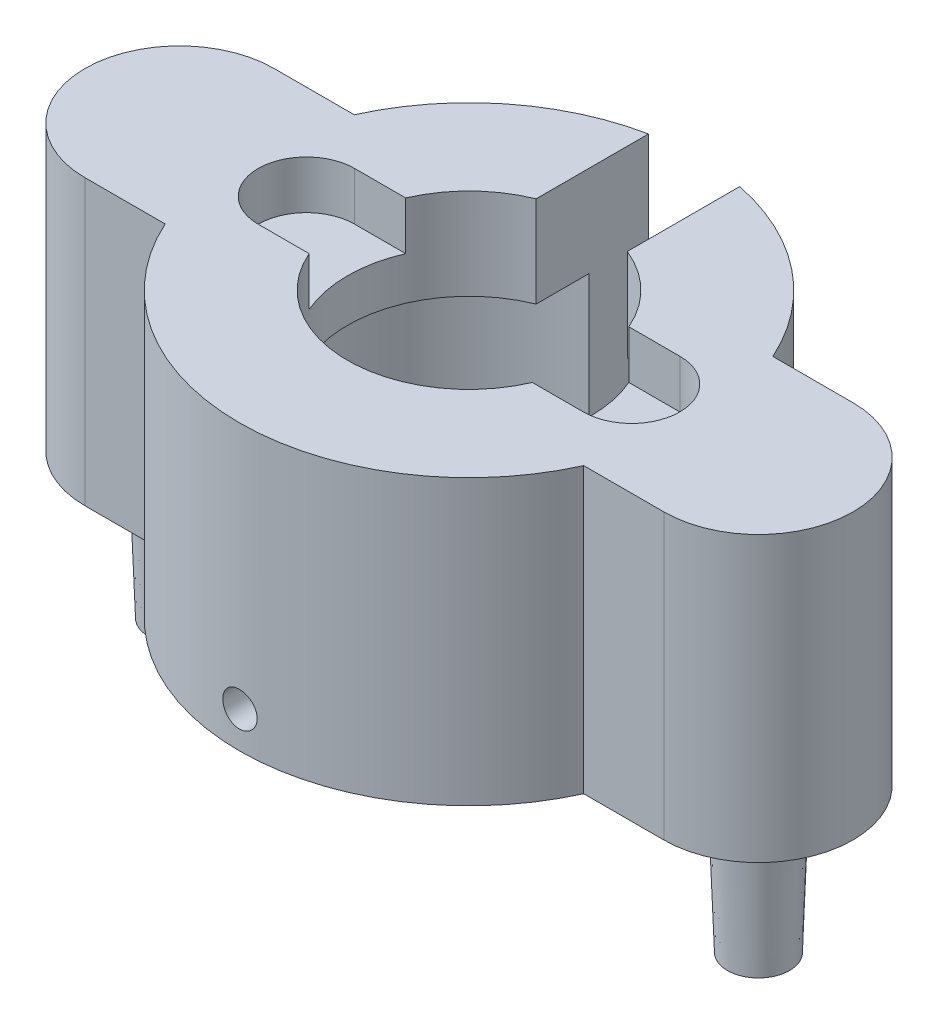
SolidWorks part; units mm, degrees
ref_plane "Front Plane" through (0, 0, 0) normal (0, 0, 1) x (1, 0, 0)
ref_plane "Top Plane" through (0, 0, 0) normal (0, 1, 0) x (1, 0, 0)
ref_plane "Right Plane" through (0, 0, 0) normal (1, 0, 0) x (0, 0, -1)
sketch "Sketch1" plane through (0, 0, 0) normal (0, 1, 0) x (1, 0, 0)
  line L0 (-19.05, 6.223) -> (-13.7723, 6.223)
  line L1 (19.05, 6.223) -> (13.7723, 6.223)
  line L2 (19.05, -6.223) -> (13.7723, -6.223)
  line L3 (-19.05, -6.223) -> (-13.7723, -6.223)
  circle A0 centre (0, 0) radius 11.303
  circle A1 centre (0, 0) radius 15.113 construction
  circle A2 centre (19.05, 0) radius 2.413 construction
  circle A3 centre (-19.05, 0) radius 2.413 construction
  circle A4 centre (19.05, 0) radius 6.223 construction
  circle A5 centre (-19.05, 0) radius 6.223 construction
  arc A6 (-19.05, 6.223) -> (-19.05, -6.223) centre (-19.05, 0) ccw
  arc A7 (19.05, 6.223) -> (19.05, -6.223) centre (19.05, 0) cw
  arc A8 (-13.7723, 6.223) -> (13.7723, 6.223) centre (0, 0) cw
  arc A9 (-13.7723, -6.223) -> (13.7723, -6.223) centre (0, 0) ccw
  dimension "D1" = 22.606
  dimension "D2" = 3.81
  dimension "D3" = 4.826
  dimension "D4" = 19.05
  dimension "D6" = 3.81
  dimension "D5" = 19.05
extrude "Boss-Extrude1" add sketch "Sketch1" along normal blind 12.7
ref_plane "Plane1" through (0, 0, 15.113) normal (0, 0, 1) x (1, 0, 0)
hole_wizard "#4-40 Tapped Hole1" positions "Sketch3" profile "Sketch4" tap size "#4-40" standard "Ansi Inch" end condition through all
sketch "Sketch3" plane through (0, 0, 15.113) normal (0, 0, 1) x (1, 0, 0)
  line L0 (-13.7723, 0) -> (13.7723, 0) construction
  point P1 (0, 2.3813)
  dimension "D1" = 2.3813
sketch "Sketch4" plane through (0, 2.3813, 15.113) normal (1, 0, 0) x (0, -1, 0)
  line L0 (0, 0) -> (0, 30.226)
  line L1 (0, 30.226) -> (1.1303, 30.226)
  line L2 (1.1303, 30.226) -> (1.1303, 0)
  line L5 (1.1303, 0) -> (0, 0)
  line L11 (0, -6.35) -> (0, 107.95) construction
  dimension "Thread Major Dia." = 2.2606
  dimension "Thru Tap Drill Depth" = 30.226
ref_plane "Plane2" through (25.273, 0, 0) normal (1, 0, 0) x (0, 0, -1)
hole_wizard "#4-40 Tapped Hole3" [suppressed] positions "Sketch8" profile "Sketch9" tap size "#4-40" standard "Ansi Inch"
sketch "Sketch8" plane through (0, 9.525, 0) normal (0, 1, 0) x (-1, 0, 0)
  point P0 (12.7, 0)
  dimension "D1" = 12.7
sketch "Sketch9" plane through (-12.7, 9.525, 0) normal (1, 0, 0) x (0, 0, 1)
  line L0 (0, 0) -> (0, 9.525)
  line L1 (0, 9.525) -> (1.1303, 9.525)
  line L2 (1.1303, 9.525) -> (1.1303, 0)
  line L5 (1.1303, 0) -> (0, 0)
  line L11 (0, -6.35) -> (0, 107.95) construction
  dimension "Thread Major Dia." = 2.2606
  dimension "Thru Tap Drill Depth" = 9.525
pattern_circular "CirPattern1" [suppressed] count 6 over 360
sketch "Sketch10" plane through (0, 0, 0) normal (0, -1, 0) x (1, 0, 0)
  circle A0 centre (-19.05, 0) radius 2.3813
  circle A1 centre (19.05, 0) radius 2.3813
  dimension "D1" = 4.7625
extrude "Boss-Extrude2" add sketch "Sketch10" along normal blind 9.525 draft 2
sketch "Sketch14" plane through (0, 12.7, 0) normal (0, 1, 0) x (1, 0, 0)
  circle A0 centre (0, 0) radius 15.113
  circle A1 centre (0, 0) radius 8
  arc M1 (-19.05, 6.223) -> (-19.05, -6.223) centre (-19.05, 0) ccw
  line M2 (-19.05, -6.223) -> (-13.7723, -6.223)
  arc M3 (-13.7723, -6.223) -> (13.7723, -6.223) centre (0, 0) ccw
  line M4 (13.7723, -6.223) -> (19.05, -6.223)
  arc M5 (19.05, -6.223) -> (19.05, 6.223) centre (19.05, 0) ccw
  line M6 (19.05, 6.223) -> (13.7723, 6.223)
  arc M7 (13.7723, 6.223) -> (-13.7723, 6.223) centre (0, 0) ccw
  line M8 (-13.7723, 6.223) -> (-19.05, 6.223)
  circle M9 centre (0, 0) radius 11.303
  dimension "D1" = 16
extrude "Boss-Extrude3" add sketch "Sketch14" along normal blind 6 contours A0 M4 M5 M6 | A0 M8 M1 M2 | A0 M3 M7 M9 | A1 M9
hole_wizard "#2 Clearance Hole1" [suppressed] positions "Sketch18" profile "Sketch17" hole size "#2" standard "Ansi Inch"
sketch "Sketch18" plane through (13.2831, 40.925, -3.013) normal (0, 1, 0) x (-1, 0, 0)
  line L0 (4.3414, 3.013) -> (-4.3019, 3.013) construction
  line L3 (13.2831, -2.1542) -> (13.2831, 2.3598) construction
  point P0 (2.5831, 3.013)
  point P10 (23.9831, 3.013)
  dimension "D1" = 21.4
sketch "Sketch17" plane through (10.7, 40.925, 0) normal (1, 0, 0) x (0, 0, 1)
  line L0 (0, 0) -> (0, 5.8126)
  line L1 (0, 5.8126) -> (1.2192, 5.08)
  line L2 (1.2192, 5.08) -> (1.2192, 0)
  line L5 (1.2192, 0) -> (0, 0)
  line L10 (0, 5.8126) -> (-1.2192, 5.08) construction
  line L11 (0, -6.35) -> (0, 107.95) construction
  dimension "Hole Dia." = 2.4384
  dimension "Hole Depth" = 5.08
  dimension "Drill Angle" = 118
sketch "Sketch19" plane through (0, 0, 0) normal (1, 0, 0) x (0, 0, -1)
  line L1 (-2.25, 14.7) -> (2.25, 14.7)
  line L2 (-2.25, 14.7) -> (-2.25, 16.7)
  line L3 (-2.25, 16.7) -> (2.25, 16.7)
  line L4 (2.25, 14.7) -> (2.25, 16.7)
  line L5 (-2.25, 14.7) -> (2.25, 16.7) construction
  line L6 (-2.25, 16.7) -> (2.25, 14.7) construction
  line L7 (0, 27.8003) -> (0, -27.8003) construction
  line L8 (6.223, 18.7) -> (-6.223, 18.7) construction
  point P0 (0, 15.7)
  dimension "D1" = 4.5
  dimension "D2" = 2
  dimension "D3" = 2
extrude "Cut-Extrude2" [suppressed] cut sketch "Sketch19" against normal blind 14
mirror "Mirror2" [suppressed] about plane through (0, 0, 0) normal (1, 0, 0)
sketch "Sketch20" plane through (0, 18.7, 0) normal (0, 1, 0) x (1, 0, 0)
  line L1 (-3, 2.1549) -> (3, 2.1549)
  line L2 (-3, 2.1549) -> (-3, 18.1483)
  line L3 (-3, 18.1483) -> (3, 18.1483)
  line L4 (3, 2.1549) -> (3, 18.1483)
  line L5 (-3, 2.1549) -> (3, 18.1483) construction
  line L6 (-3, 18.1483) -> (3, 2.1549) construction
  point P0 (0, 10.1516)
  dimension "D1" = 6
extrude "Cut-Extrude3" cut sketch "Sketch20" against normal through all
sketch "Sketch21" plane through (0, 18.7, 0) normal (0, 1, 0) x (1, 0, 0)
  line L0 (-12.3499, 0) -> (14.2739, 0) construction
  line L1 (0, 16.6195) -> (0, -10.2643) construction
  line L2 (-10.7, 0) -> (10.7, 0) construction
  line L3 (-10.7, 3.175) -> (10.7, 3.175)
  line L4 (-10.7, -3.175) -> (10.7, -3.175)
  arc A0 (-10.7, 3.175) -> (-10.7, -3.175) centre (-10.7, 0) ccw
  arc A1 (10.7, -3.175) -> (10.7, 3.175) centre (10.7, 0) ccw
  point P7 (0, 0)
  dimension "D2" = 3.175
  dimension "D1" = 21.4
extrude "Cut-Extrude4" cut sketch "Sketch21" against normal blind 3.175
